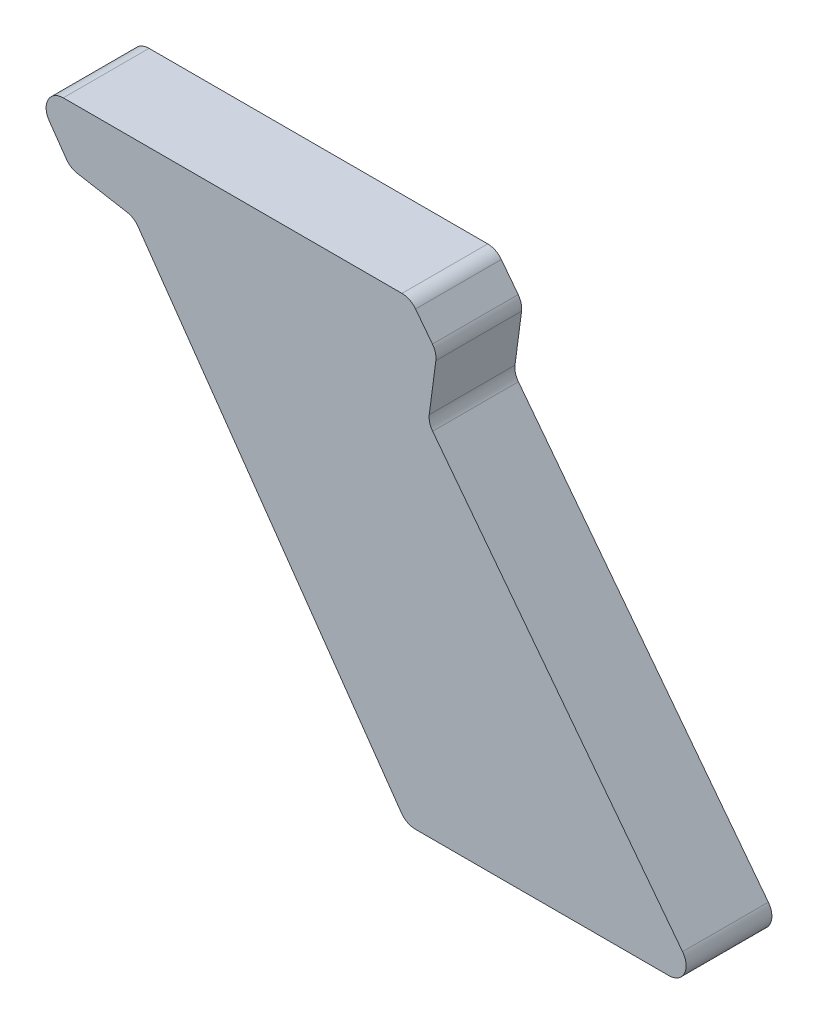
SolidWorks part; units mm, degrees
ref_plane "Plane1" through (0, 0, 0) normal (0, 0, 1) x (1, 0, 0)
ref_plane "Plane2" through (0, 0, 0) normal (0, 1, 0) x (1, 0, 0)
ref_plane "Plane3" through (0, 0, 0) normal (1, 0, 0) x (0, 0, -1)
sketch "Sketch1" plane through (0, 0, 0) normal (0, 0, 1) x (1, 0, 0)
  line L0 (-3.7033, 4.8263) -> (-47.4187, 61.7972)
  line L1 (-48.013, 64.0151) -> (-46.8606, 72.768)
  line L2 (-47.4549, 74.9859) -> (-50.4018, 78.8263)
  line L3 (-52.7818, 80) -> (-112.0199, 80)
  line L4 (-114.4773, 75.2793) -> (-111.4935, 71.0179)
  line L5 (-109.557, 69.7842) -> (-100.8627, 68.2512)
  line L6 (-98.9261, 67.0175) -> (-52.8958, 1.2793)
  line L7 (-50.4383, 0) -> (-6.0834, 0)
  arc A0 (-50.4018, 78.8263) -> (-52.7818, 80) centre (-52.7818, 77) ccw
  arc A1 (-46.8606, 72.768) -> (-47.4549, 74.9859) centre (-49.8349, 73.1596) ccw
  arc A2 (-47.4187, 61.7972) -> (-48.013, 64.0151) centre (-45.0386, 63.6235) cw
  arc A3 (-6.0834, 0) -> (-3.7033, 4.8263) centre (-6.0834, 3) ccw
  arc A4 (-52.8958, 1.2793) -> (-50.4383, 0) centre (-50.4383, 3) ccw
  arc A5 (-100.8627, 68.2512) -> (-98.9261, 67.0175) centre (-101.3836, 65.2968) cw
  arc A6 (-111.4935, 71.0179) -> (-109.557, 69.7842) centre (-109.036, 72.7386) ccw
  arc A7 (-112.0199, 80) -> (-114.4773, 75.2793) centre (-112.0199, 77) ccw
  point P13 (-46.6984, 74)
  point P18 (0, 0)
  point P21 (-52, 0)
  point P26 (-110.7807, 70)
  dimension "D11" = 3
  dimension "D1" = 52.5
  dimension "D2" = 2.5
  dimension "D3" = 52
  dimension "D4" = 80
  dimension "D5" = 8
  dimension "D6" = 8
  dimension "D7" = 6
  dimension "D8" = 10
  dimension "D9" = 45
  dimension "D10" = 45
extrude "Extrude1" add sketch "Sketch1" along normal blind 15
